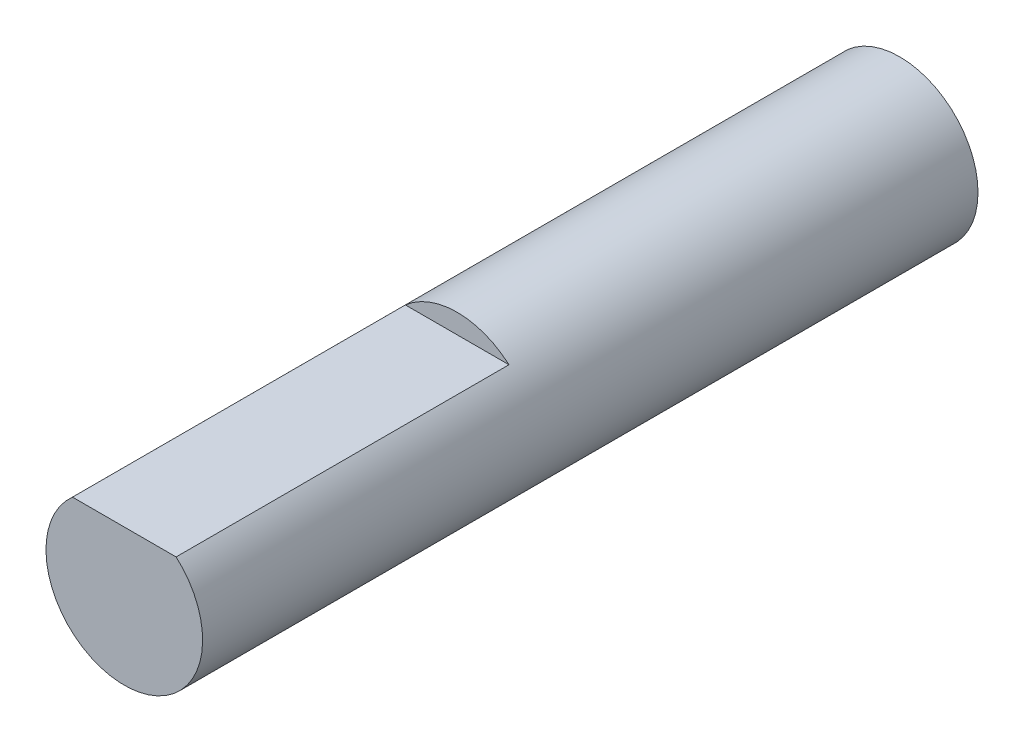
SolidWorks part; units mm, degrees
ref_plane "Front Plane" through (0, 0, 0) normal (0, 0, 1) x (1, 0, 0)
ref_plane "Top Plane" through (0, 0, 0) normal (0, 1, 0) x (1, 0, 0)
ref_plane "Right Plane" through (0, 0, 0) normal (1, 0, 0) x (0, 0, -1)
sketch "Sketch1" plane through (0, 0, 0) normal (0, 0, 1) x (1, 0, 0)
  circle A0 centre (0, 0) radius 2
  dimension "D1" = 4
extrude "Boss-Extrude1" add sketch "Sketch1" along normal blind 19.8
sketch "Sketch2" plane through (0, 0, 19.8) normal (0, 0, 1) x (1, 0, 0)
  line L0 (0, 0) -> (0, 1.5) construction
  line L2 (-1.3229, 1.5) -> (1.3229, 1.5)
  circle A0 centre (0, 0) radius 2 construction
  dimension "D1" = 1.5
extrude "Cut-Extrude1" cut sketch "Sketch2" against normal blind 8.5 and the other way through all
